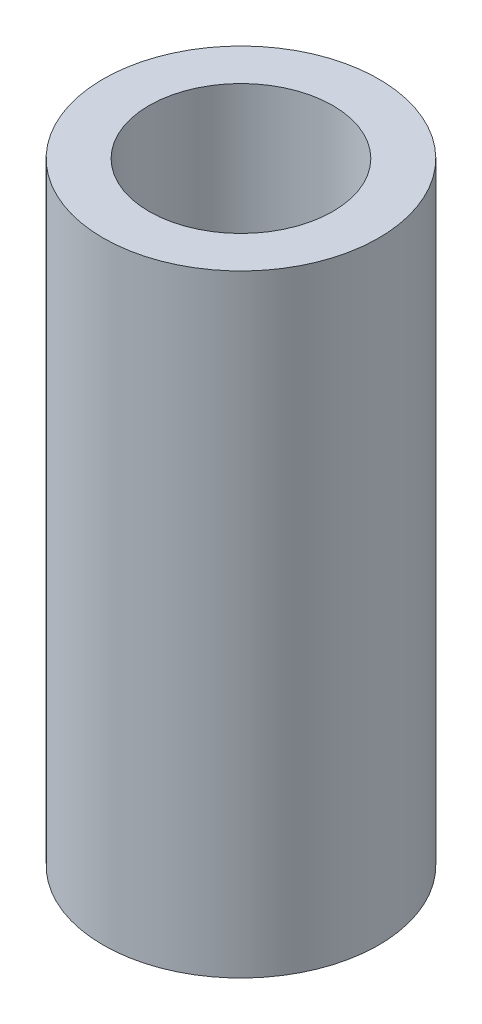
SolidWorks part; units mm, degrees
ref_plane "Front Plane" through (0, 0, 0) normal (0, 0, 1) x (1, 0, 0)
ref_plane "Top Plane" through (0, 0, 0) normal (0, 1, 0) x (1, 0, 0)
ref_plane "Right Plane" through (0, 0, 0) normal (1, 0, 0) x (0, 0, -1)
sketch "Sketch2" plane through (0, 0, 0) normal (0, 1, 0) x (1, 0, 0)
  circle A0 centre (0, 0) radius 4.5
  dimension "D1" = 9
extrude "Boss-Extrude1" add sketch "Sketch2" along normal blind 20
sketch "Sketch3" plane through (0, 20, 0) normal (0, 1, 0) x (1, 0, 0)
  circle A0 centre (0, 0) radius 3
  dimension "D1" = 6
extrude "Cut-Extrude1" cut sketch "Sketch3" against normal blind 10
sketch "Sketch4" plane through (0, 0, 0) normal (0, -1, 0) x (1, 0, 0)
  circle A0 centre (0, 0) radius 2.5
  dimension "D1" = 5
extrude "Cut-Extrude2" cut sketch "Sketch4" against normal blind 10
